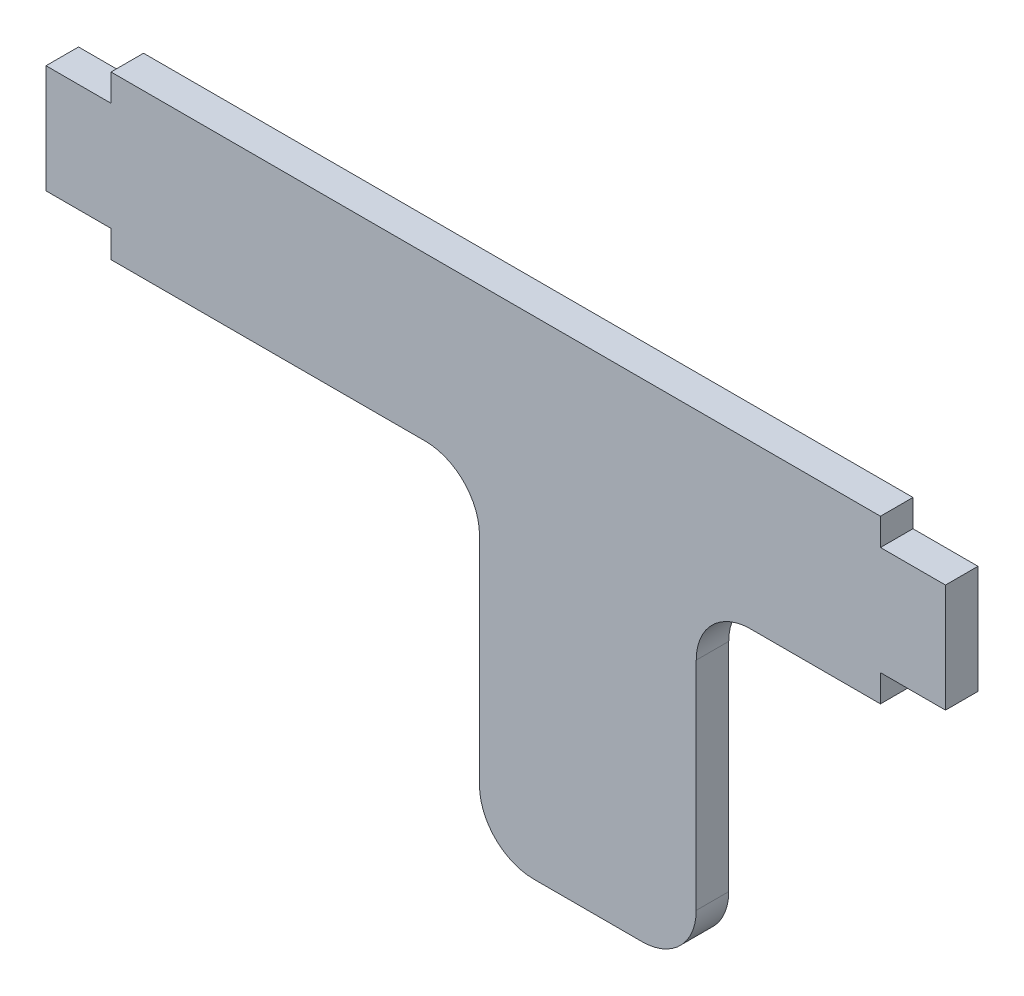
SolidWorks part; units mm, degrees
material "MDF"
ref_plane "Plano frontal" through (0, 0, 0) normal (0, 0, 1) x (1, 0, 0)
ref_plane "Plano superior" through (0, 0, 0) normal (0, 1, 0) x (1, 0, 0)
ref_plane "Plano direito" through (0, 0, 0) normal (1, 0, 0) x (0, 0, -1)
sketch "Esboço1" plane through (0, 0, 0) normal (0, 0, 1) x (1, 0, 0)
  line L0 (0, 0) -> (0, 7.5) construction
  line L1 (35.5, -7.5) -> (-35.5, -7.5)
  line L2 (35.5, -7.5) -> (35.5, 7.5)
  line L3 (35.5, 7.5) -> (-35.5, 7.5)
  line L4 (-35.5, -7.5) -> (-35.5, 7.5)
  line L5 (35.5, -7.5) -> (-35.5, 7.5) construction
  line L6 (35.5, 7.5) -> (-35.5, -7.5) construction
  line L7 (18.5, -37.5) -> (-1.5, -37.5)
  line L8 (18.5, -37.5) -> (18.5, -7.5)
  line L9 (18.5, -7.5) -> (-1.5, -7.5)
  line L10 (-1.5, -37.5) -> (-1.5, -7.5)
  line L11 (18.5, -37.5) -> (-1.5, -7.5) construction
  line L12 (18.5, -7.5) -> (-1.5, -37.5) construction
  line L13 (-41.5, -5) -> (-35.5, -5)
  line L14 (-41.5, -5) -> (-41.5, 5)
  line L15 (-41.5, 5) -> (-35.5, 5)
  line L16 (-35.5, -5) -> (-35.5, 5)
  line L17 (-41.5, -5) -> (-35.5, 5) construction
  line L18 (-41.5, 5) -> (-35.5, -5) construction
  line L19 (41.5, 5) -> (35.5, 5)
  line L20 (35.5, -5) -> (35.5, 5)
  line L21 (41.5, -5) -> (35.5, -5)
  line L22 (41.5, -5) -> (41.5, 5)
  point P0 (0, 0)
  point P6 (8.5, -22.5)
  point P12 (-38.5, 0)
  dimension "D1" = 71
  dimension "D2" = 30
  dimension "D3" = 15
  dimension "D4" = 20
  dimension "D5" = 6
  dimension "D6" = 10
  dimension "D7" = 33
extrude "Ressalto-extrusão1" add sketch "Esboço1" along normal blind 3 contours L4 L1 L2 L3 | L10 L7 L8 L1 | L21 L22 L19 L2 | L15 L14 L13 L4
fillet "Filete1" radius 5 4 edges at (18.5, -37.5, 1.5) (-1.5, -37.5, 1.5) (-1.5, -7.5, 1.5) (18.5, -7.5, 1.5)
